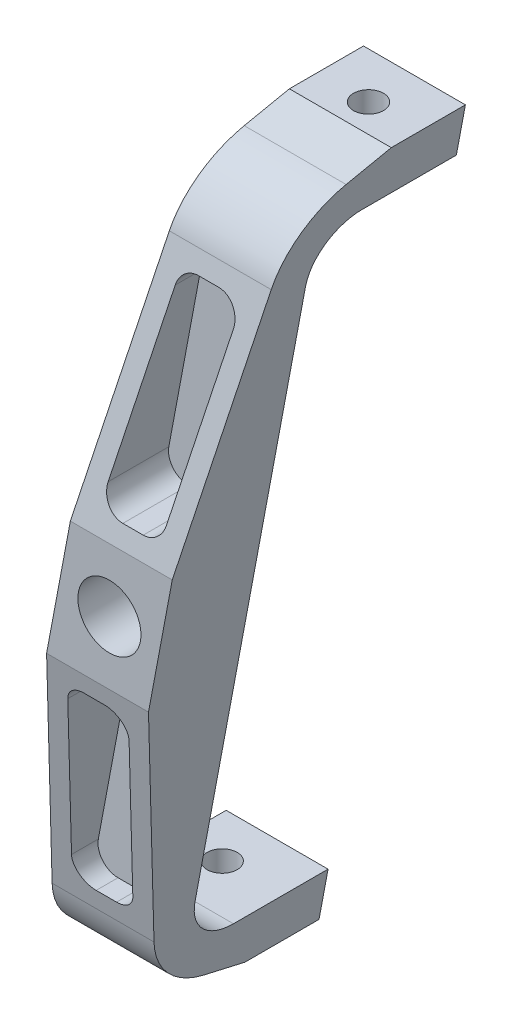
SolidWorks part; units mm, degrees
other "Markup1"
sketch "Sketch6" plane through (39.3536, 123.4271, -45) normal (0.998, 0.0328, -0.0532) x (-0.0595, 0.2351, -0.9701)
other "Markup2"
sketch "Sketch7" plane through (39.3536, 123.4271, -45) normal (0.9999, 0.0057, -0.0131) x (0.0031, -0.9818, -0.1901)
other "Markup4"
sketch "Sketch9" plane through (-39.3536, 123.4271, 27) normal (-0.9915, 0.1233, 0.0413) x (-0.1205, -0.9906, 0.0646)
material "6061-T6 (SS)"
ref_plane "Front Plane" through (0, 0, 0) normal (0, 0, 1) x (1, 0, 0)
ref_plane "Top Plane" through (0, 0, 0) normal (0, 1, 0) x (1, 0, 0)
ref_plane "Right Plane" through (0, 0, 0) normal (1, 0, 0) x (0, 0, -1)
sketch "Sketch1" plane through (0, 0, 0) normal (0, 0, 1) x (1, 0, 0)
  line L0 (0, 203) -> (0, -203) construction
  line L1 (0, -266) -> (0, -203) construction
  line L2 (0, -266) -> (-50, -266) construction
  line L3 (50, 266) -> (-50, -266) construction
  line L8 (-23.7518, -126.3598) -> (23.7518, 126.3598) construction
  line L9 (-7.0476, -123.4271) -> (39.3536, 123.4271)
  line L14 (-39.3536, -123.4271) -> (7.0476, 123.4271)
  line L15 (39.3536, 123.4271) -> (7.0476, 123.4271)
  line L16 (-39.3536, -123.4271) -> (-7.0476, -123.4271)
  line L17 (-39.3536, -123.4271) -> (8.1501, 129.2925) construction
  line L19 (-8.1501, -129.2925) -> (39.3536, 123.4271) construction
  circle A1 centre (0, 0) radius 10
  circle A2 centre (0, 0) radius 170.5 construction
  point P6 (0, 0)
  point P10 (0, -170.5)
  point P12 (0, 0)
  point P16 (0, -189.8)
  point P17 (0, 0)
  dimension "D4" = 341
  dimension "D9" = 20
  dimension "D1" = 203
  dimension "D2" = 63
  dimension "D3" = 50
  dimension "D5" = 95.5
  dimension "D6" = 76.2
  dimension "D7" = 15.875
  dimension "D8" = 15.875
extrude "Boss-Extrude1" add sketch "Sketch1" along normal blind 28.5
sketch "Sketch2" plane through (0, 0, 0) normal (0, 0, -1) x (-1, 0, 0)
  line L0 (-36.4889, 108.1871) -> (-4.1829, 108.1871)
  line L1 (4.1829, -108.1871) -> (36.4889, -108.1871)
  line L4 (-7.0476, 123.4271) -> (-39.3536, 123.4271)
  line L5 (-39.3536, 123.4271) -> (7.0476, -123.4271)
  line L6 (7.0476, -123.4271) -> (39.3536, -123.4271)
  line L7 (39.3536, -123.4271) -> (-7.0476, 123.4271)
  line L8 (-7.0476, 123.4271) -> (-39.3536, 123.4271)
  line L9 (-39.3536, 123.4271) -> (7.0476, -123.4271)
  line L10 (7.0476, -123.4271) -> (39.3536, -123.4271)
  line L11 (39.3536, -123.4271) -> (-7.0476, 123.4271)
  line M7 (-7.0476, 123.4271) -> (-39.3536, 123.4271)
  line M8 (-39.3536, 123.4271) -> (7.0476, -123.4271)
  line M9 (7.0476, -123.4271) -> (39.3536, -123.4271)
  line M10 (39.3536, -123.4271) -> (-7.0476, 123.4271)
  dimension "D2" = 15.24
  dimension "D3" = 15.24
  dimension "D1" = 0
extrude "Boss-Extrude2" add sketch "Sketch2" along normal blind 45 contours L0 M8 M10 M7 | L1 M8 M9 M10
sketch "Sketch4" plane through (0, 123.4271, 0) normal (0, 1, 0) x (1, 0, 0)
  line L0 (23.2006, -28.5) -> (23.2006, 45) construction
  line L1 (0, 30.433) -> (85.2766, 30.433) construction
  line L2 (0, 30.433) -> (85.2766, 30.433)
  line L4 (39.3536, -28.5) -> (39.3536, 45)
  line L5 (39.3536, 45) -> (7.0476, 45)
  line L6 (7.0476, 45) -> (7.0476, -28.5)
  line L7 (7.0476, -28.5) -> (39.3536, -28.5)
  line L8 (39.3536, -28.5) -> (39.3536, 45)
  line L9 (39.3536, 45) -> (7.0476, 45)
  line L10 (7.0476, 45) -> (7.0476, -28.5)
  line L11 (7.0476, -28.5) -> (39.3536, -28.5)
  circle A0 centre (23.2006, 30.433) radius 4.7625
  point P6 (23.2006, 30.433)
  dimension "D1" = 0
extrude "Cut-Extrude1" cut sketch "Sketch4" against normal blind 30 contours L0 L2 A0 | L2 L0 A0 | A0 L0 L2 | L0 A0 L2
pattern_circular "CirPattern1" count 2 over 360 about axis through (0, 0, -30.433) along (0, 1, 0) of "Cut-Extrude1"
chamfer "Chamfer1" distance 50 angle 15 2 edges at (-23.2006, -123.4271, 28.5) (23.2006, 123.4271, 28.5)
fillet "Fillet3" radius 15 2 edges at (20.3359, 108.1871, 0) (-20.3359, -108.1871, 0)
chamfer "Chamfer2" distance 90 angle 8 2 edges at (-20.6823, -110.0297, 28.5) (20.6823, 110.0297, 28.5)
sketch "Sketch10" plane through (0, 0, 0) normal (1, 0, 0) x (0, 0, -1)
  line L0 (-28.5, 20.0297) -> (-11.939, 98.8475)
  line L1 (-28.5, 20.0297) -> (-33.9568, 23.5224)
  line L2 (-33.9568, 23.5224) -> (-24.6981, 128.3877)
  line L3 (-24.6981, 128.3877) -> (7.8754, 119.7764)
  line L5 (21.5, 123.4271) -> (-15.3564, 113.5515) construction
  line L6 (21.5, 123.4271) -> (-15.3564, 113.5515) construction
  arc A0 (15, 108.1871) -> (0, 93.1871) centre (15, 93.1871) ccw construction
  arc A1 (15, 108.1871) -> (0, 93.1871) centre (15, 93.1871) ccw construction
  arc A2 (7.8754, 119.7764) -> (-11.939, 98.8475) centre (15, 93.1871) ccw
  point P14 (7.8754, 119.7764)
extrude "Cut-Extrude2" cut sketch "Sketch10" against normal through all both and the other way through all
mirror "Mirror1" about plane through (0, 0, 0) normal (0, 1, 0) of "Cut-Extrude2"
sketch "Sketch11" plane through (0, 0, 28.5) normal (0, 0, 1) x (1, 0, 0)
  line L0 (2.4273, 98.8475) -> (34.7334, 98.8475) construction
  line L1 (2.4273, 98.8475) -> (34.7334, 98.8475) construction
  line L2 (34.7334, 98.8475) -> (19.918, 20.0297) construction
  line L3 (34.7334, 98.8475) -> (19.918, 20.0297) construction
  line L4 (-12.388, 20.0297) -> (-19.918, -20.0297)
  line L5 (-19.918, -20.0297) -> (12.388, -20.0297)
  line L6 (12.388, -20.0297) -> (19.918, 20.0297)
  line L7 (19.918, 20.0297) -> (-12.388, 20.0297)
  line L8 (-12.388, 20.0297) -> (-19.918, -20.0297)
  line L10 (12.388, -20.0297) -> (19.918, 20.0297)
  line L11 (19.918, 20.0297) -> (-12.388, 20.0297) construction
  line L12 (-12.388, 20.0297) -> (2.4273, 98.8475) construction
  line L13 (-12.388, 20.0297) -> (2.4273, 98.8475) construction
  line L14 (-4.9804, 59.4386) -> (27.3257, 59.4386) construction
  line L15 (18.5804, 98.8475) -> (3.765, 20.0297) construction
  line L16 (-6.1473, 18.8566) -> (-5.9268, 20.0297)
  line L17 (7.6949, 92.4975) -> (27.0786, 92.4975)
  line L18 (27.0786, 92.4975) -> (14.6504, 26.3797)
  line L23 (-4.7332, 26.3797) -> (7.6949, 92.4975)
  line L24 (-34.7334, -98.8475) -> (-2.4273, -98.8475) construction
  line L25 (14.6504, 26.3797) -> (-4.7332, 26.3797)
  line L26 (-6.1473, 18.8566) -> (7.6949, 92.4975) construction
  line L27 (27.0786, 92.4975) -> (13.6773, 21.2027) construction
  line L28 (-2.4273, -98.8475) -> (12.388, -20.0297) construction
  line L29 (-19.918, -20.0297) -> (-34.7334, -98.8475) construction
  line L30 (-19.918, -20.0297) -> (12.388, -20.0297) construction
  line L31 (-34.7334, -98.8475) -> (-2.4273, -98.8475)
  line L32 (-2.4273, -98.8475) -> (12.388, -20.0297)
  line L33 (-19.918, -20.0297) -> (-34.7334, -98.8475)
  line L34 (-19.918, -20.0297) -> (12.388, -20.0297)
  line L35 (-14.6504, -26.3797) -> (4.7332, -26.3797)
  line L36 (-7.6949, -92.4975) -> (4.7332, -26.3797)
  line L37 (-27.0786, -92.4975) -> (-7.6949, -92.4975)
  line L38 (-14.6504, -26.3797) -> (-27.0786, -92.4975)
  point P18 (27.5728, 26.3797)
  point P19 (-17.6556, 26.3797)
  dimension "D2" = 6.35
  dimension "D1" = 0
  dimension "D3" = 6.35
extrude "Cut-Extrude4" cut sketch "Sketch11" against normal offset from surface (22.15 mm away) 6.35 contours L25 L18 L17 L23 | L35 L38 L37 L36 up to face at (0, 0, 0)
fillet "Fillet6" radius 6.35 8 edges at (14.6504, 26.3797, 16.7579) (-4.7332, 26.3797, 16.7579) (27.0786, 92.4975, 9.8116) (7.6949, 92.4975, 9.8116) (-7.6949, -92.4975, 9.8116) (-27.0786, -92.4975, 9.8116) (4.7332, -26.3797, 16.7579) (-14.6504, -26.3797, 16.7579)
